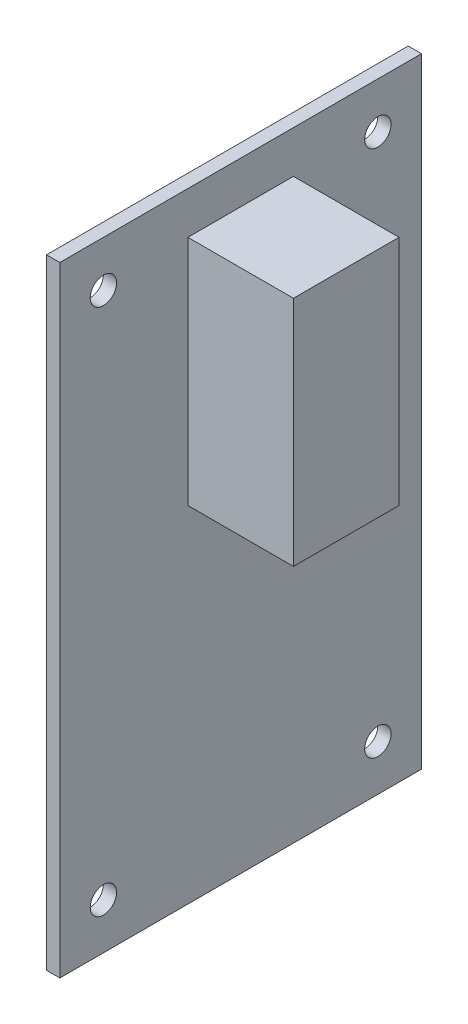
SolidWorks part; units mm, degrees
ref_plane "Front Plane" through (0, 0, 0) normal (0, 0, 1) x (1, 0, 0)
ref_plane "Top Plane" through (0, 0, 0) normal (0, 1, 0) x (1, 0, 0)
ref_plane "Right Plane" through (0, 0, 0) normal (1, 0, 0) x (0, 0, -1)
sketch "Sketch1" plane through (0, 0, 0) normal (1, 0, 0) x (0, 0, -1)
  line L1 (0, 0) -> (43.5102, 0)
  line L2 (0, 0) -> (0, 74.549)
  line L3 (0, 74.549) -> (43.5102, 74.549)
  line L4 (43.5102, 0) -> (43.5102, 74.549)
  dimension "D1" = 43.5102
  dimension "D2" = 74.549
extrude "Extrude1" add sketch "Sketch1" along normal blind 1.6002
sketch "Sketch2" plane through (1.6002, 0, 0) normal (1, 0, 0) x (0, 0, -1)
  line L0 (21.7551, 74.549) -> (21.7551, 0) construction
  line L1 (43.5102, 74.549) -> (0, 74.549) construction
  line L2 (0, 0) -> (43.5102, 0) construction
  line L3 (0, 37.2745) -> (43.5102, 37.2745) construction
  line L4 (0, 74.549) -> (0, 0) construction
  line L5 (43.5102, 0) -> (43.5102, 74.549) construction
  circle A0 centre (5.2451, 69.0245) radius 1.5875
  circle A1 centre (38.2651, 69.0245) radius 1.5875
  circle A2 centre (38.2651, 5.5245) radius 1.5875
  circle A3 centre (5.2451, 5.5245) radius 1.5875
  dimension "D1" = 3.175
  dimension "D2" = 16.51
  dimension "D3" = 31.75
extrude "Cut-Extrude1" cut sketch "Sketch2" against normal through all
sketch "Sketch3" plane through (1.6002, 0, 0) normal (1, 0, 0) x (0, 0, -1)
  line L0 (21.7551, 74.549) -> (21.7551, 0) construction
  line L1 (43.5102, 74.549) -> (0, 74.549) construction
  line L2 (0, 0) -> (43.5102, 0) construction
  line L4 (15.4051, 69.469) -> (28.1051, 69.469)
  line L5 (15.4051, 69.469) -> (15.4051, 41.529)
  line L6 (15.4051, 41.529) -> (28.1051, 41.529)
  line L7 (28.1051, 69.469) -> (28.1051, 41.529)
  dimension "D1" = 12.7
  dimension "D2" = 27.94
  dimension "D3" = 6.35
  dimension "D4" = 5.08
extrude "Extrude2" add sketch "Sketch3" along normal blind 12.7
